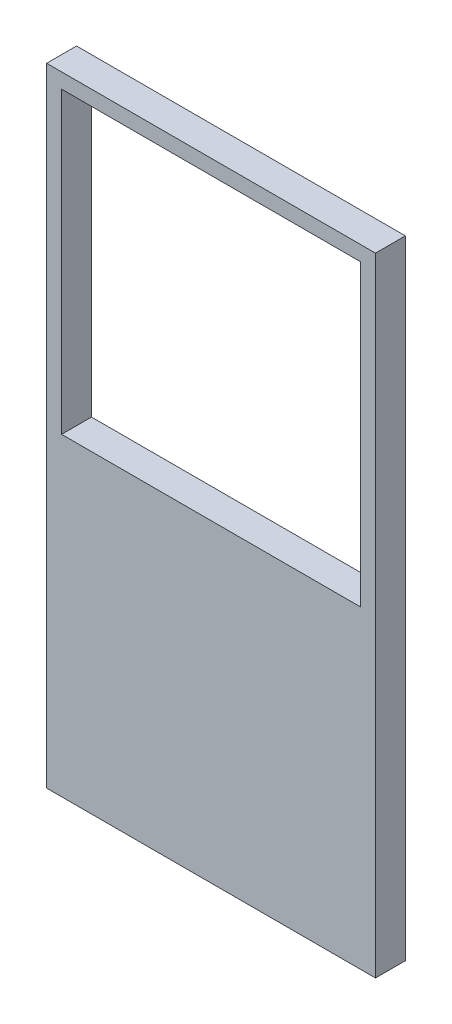
SolidWorks part; units mm, degrees
ref_plane "Front Plane" through (0, 0, 0) normal (0, 0, 1) x (1, 0, 0)
ref_plane "Top Plane" through (0, 0, 0) normal (0, 1, 0) x (1, 0, 0)
ref_plane "Right Plane" through (0, 0, 0) normal (1, 0, 0) x (0, 0, -1)
sketch "Sketch1" plane through (0, 0, 0) normal (0, 0, 1) x (1, 0, 0)
  line L1 (12.7, 12.7) -> (-12.7, 12.7)
  line L2 (12.7, 12.7) -> (12.7, -12.7)
  line L3 (12.7, -12.7) -> (-12.7, -12.7)
  line L4 (-12.7, 12.7) -> (-12.7, -12.7)
  line L5 (12.7, 12.7) -> (-12.7, -12.7) construction
  line L6 (12.7, -12.7) -> (-12.7, 12.7) construction
  point P0 (0, 0)
  dimension "D1" = 25.4
extrude "Extrude-Thin1" add sketch "Sketch1" along normal mid plane 2.54 thin
sketch "Sketch2" plane through (0, 0, 1.27) normal (0, 0, 1) x (1, 0, 0)
  line L1 (-13.97, -13.97) -> (13.97, -13.97)
  line L2 (-13.97, -13.97) -> (-13.97, -39.37)
  line L3 (-13.97, -39.37) -> (13.97, -39.37)
  line L4 (13.97, -13.97) -> (13.97, -39.37)
  line L5 (13.97, -13.97) -> (13.97, 13.97) construction
  dimension "D1" = 25.4
extrude "Boss-Extrude1" add sketch "Sketch2" against normal through all
